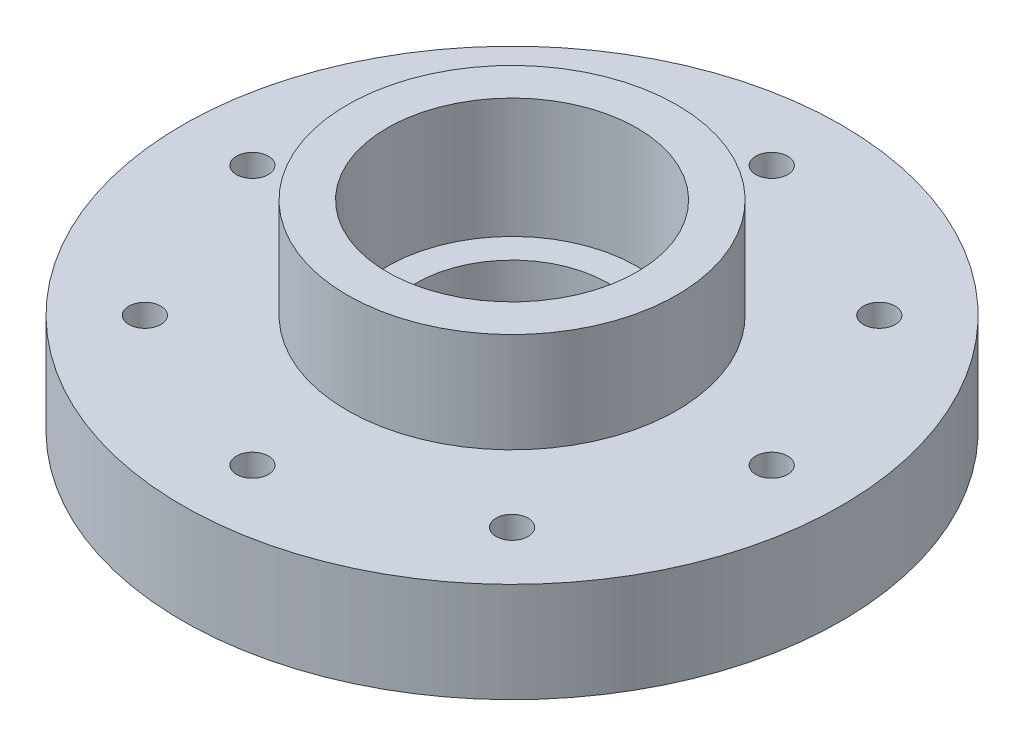
SolidWorks part; units mm, degrees
material "Plain Carbon Steel"
ref_plane "Front Plane" through (0, 0, 0) normal (0, 0, 1) x (1, 0, 0)
ref_plane "Top Plane" through (0, 0, 0) normal (0, 1, 0) x (1, 0, 0)
ref_plane "Right Plane" through (0, 0, 0) normal (1, 0, 0) x (0, 0, -1)
sketch "Sketch1" plane through (0, 0, 0) normal (0, 1, 0) x (1, 0, 0)
  circle A0 centre (0, 0) radius 56 construction
  circle A1 centre (0, 0) radius 82.5 construction
  circle A2 centre (65, 0) radius 4 construction
  circle A3 centre (65, 0) radius 4
  circle A4 centre (45.9619, -45.9619) radius 4 construction
  circle A5 centre (0, -65) radius 4 construction
  circle A6 centre (-45.9619, -45.9619) radius 4 construction
  circle A7 centre (-65, 0) radius 4 construction
  circle A11 centre (45.9619, -45.9619) radius 4
  circle A12 centre (0, -65) radius 4
  circle A13 centre (-45.9619, -45.9619) radius 4
  circle A14 centre (-65, 0) radius 4
  circle A15 centre (-45.9619, 45.9619) radius 4
  circle A16 centre (0, 65) radius 4
  circle A17 centre (45.9619, 45.9619) radius 4
  circle A18 centre (0, 0) radius 55 construction
  circle A19 centre (45.9619, 45.9619) radius 4 construction
  circle A20 centre (0, 65) radius 4 construction
  circle A21 centre (-45.9619, 45.9619) radius 4 construction
  dimension "D1" = 165
  dimension "D2" = 13.5
  dimension "D3" = 1
sketch "Sketch2" plane through (0, 0, 0) normal (0, 0, 1) x (1, 0, 0)
  line L0 (0, 0) -> (0, 67.5538) construction
  line L1 (82.5, 0) -> (56, 0)
  line L2 (82.5, 0) -> (-82.5, 0) construction
  line L3 (56, 0) -> (-56, 0) construction
  line L7 (24, 20) -> (31.2565, 20)
  line L8 (82.5, 25) -> (82.5, 0)
  line L10 (82.5, 25) -> (41.2565, 25)
  line L12 (24, 20) -> (24, 6)
  line L15 (56, 0) -> (56, 6)
  line L16 (56, 6) -> (24, 6)
  line L17 (31.2565, 20) -> (31.2565, 50)
  line L18 (31.2565, 50) -> (41.2565, 50)
  line L20 (41.2565, 25) -> (41.2565, 50)
  dimension "D1" = 50
  dimension "D2" = 20
  dimension "D3" = 6
  dimension "D4" = 112
  dimension "D5" = 62.5129
  dimension "D6" = 48
  dimension "D7" = 10
  dimension "D8" = 14
  dimension "D9" = 25
revolve "Revolve1" add sketch "Sketch2" angle 360 about L0
sketch "Sketch3" plane through (0, 0, 0) normal (0, -1, 0) x (1, 0, 0)
  circle A1 centre (65, 0) radius 4
  circle A2 centre (65, 0) radius 4
  circle A3 centre (45.9619, -45.9619) radius 4
  circle A4 centre (45.9619, -45.9619) radius 4
  circle A5 centre (0, -65) radius 4
  circle A6 centre (0, -65) radius 4
  circle A7 centre (-45.9619, -45.9619) radius 4
  circle A8 centre (-45.9619, -45.9619) radius 4
  circle A9 centre (-65, 0) radius 4
  circle A10 centre (-65, 0) radius 4
  circle A11 centre (-45.9619, 45.9619) radius 4
  circle A12 centre (-45.9619, 45.9619) radius 4
  circle A13 centre (0, 65) radius 4
  circle A14 centre (0, 65) radius 4
  circle A15 centre (45.9619, 45.9619) radius 4
  circle A16 centre (45.9619, 45.9619) radius 4
  dimension "D1" = 0
  dimension "D2" = 0
  dimension "D3" = 0
  dimension "D4" = 0
  dimension "D5" = 0
  dimension "D6" = 0
  dimension "D7" = 0
  dimension "D8" = 0
extrude "Cut-Extrude2" cut sketch "Sketch3" against normal through all
